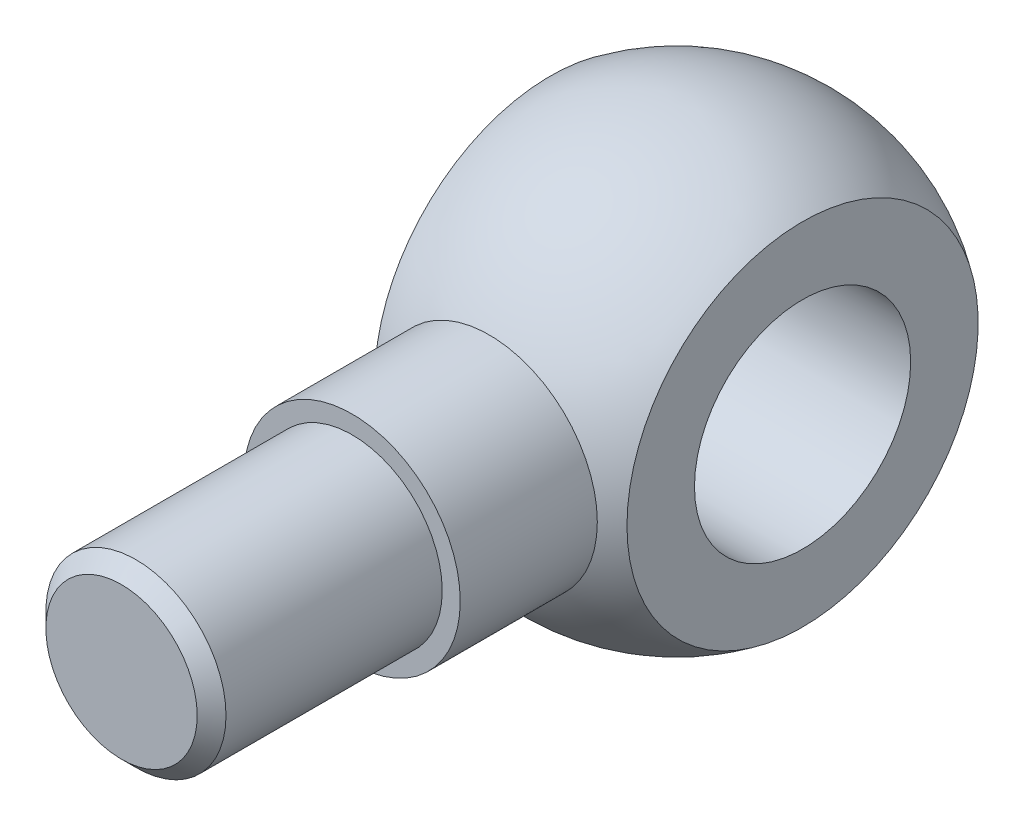
SolidWorks part; units mm, degrees
ref_plane "Přední rovina" through (0, 0, 0) normal (0, 0, 1) x (1, 0, 0)
ref_plane "Vrchní rovina" through (0, 0, 0) normal (0, 1, 0) x (1, 0, 0)
ref_plane "Pravá rovina" through (0, 0, 0) normal (1, 0, 0) x (0, 0, -1)
sketch "Skica1" plane through (0, 0, 0) normal (0, 0, 1) x (1, 0, 0)
  line L0 (-37.4733, 0) -> (35.0467, 0) construction
  line L1 (-17.5, 24.367) -> (-17.5, -24.367)
  line L2 (17.5, 24.367) -> (17.5, -24.367)
  line L3 (-17.5, 15) -> (17.5, 15)
  line L4 (-17.5, -15) -> (17.5, -15)
  arc A0 (-17.5, -24.367) -> (17.5, -24.367) centre (0, 0) ccw
  arc A1 (17.5, 24.367) -> (-17.5, 24.367) centre (0, 0) ccw
  dimension "D3" = 30
  dimension "D1" = 35
  dimension "D2" = 30
revolve "Rotovat1" add sketch "Skica1" angle 360 about L0
ref_plane "Rovina1" through (0, 0, 45) normal (0, 0, 1) x (1, 0, 0)
sketch "Skica4" plane through (0, 0, 45) normal (0, 0, 1) x (1, 0, 0)
  circle A0 centre (0, 0) radius 15
  dimension "D1" = 30
extrude "Přidat vysunutím1" add sketch "Skica4" against normal up to surface (19.0192 mm away)
sketch "Skica5" plane through (0, 0, 45) normal (0, 0, 1) x (1, 0, 0)
  circle A0 centre (0, 0) radius 12.5
  dimension "D1" = 25
extrude "Přidat vysunutím2" add sketch "Skica5" along normal blind 32
chamfer "Zkosení1" distance 2 angle 45 1 edges at (12.5, 0, 77)
